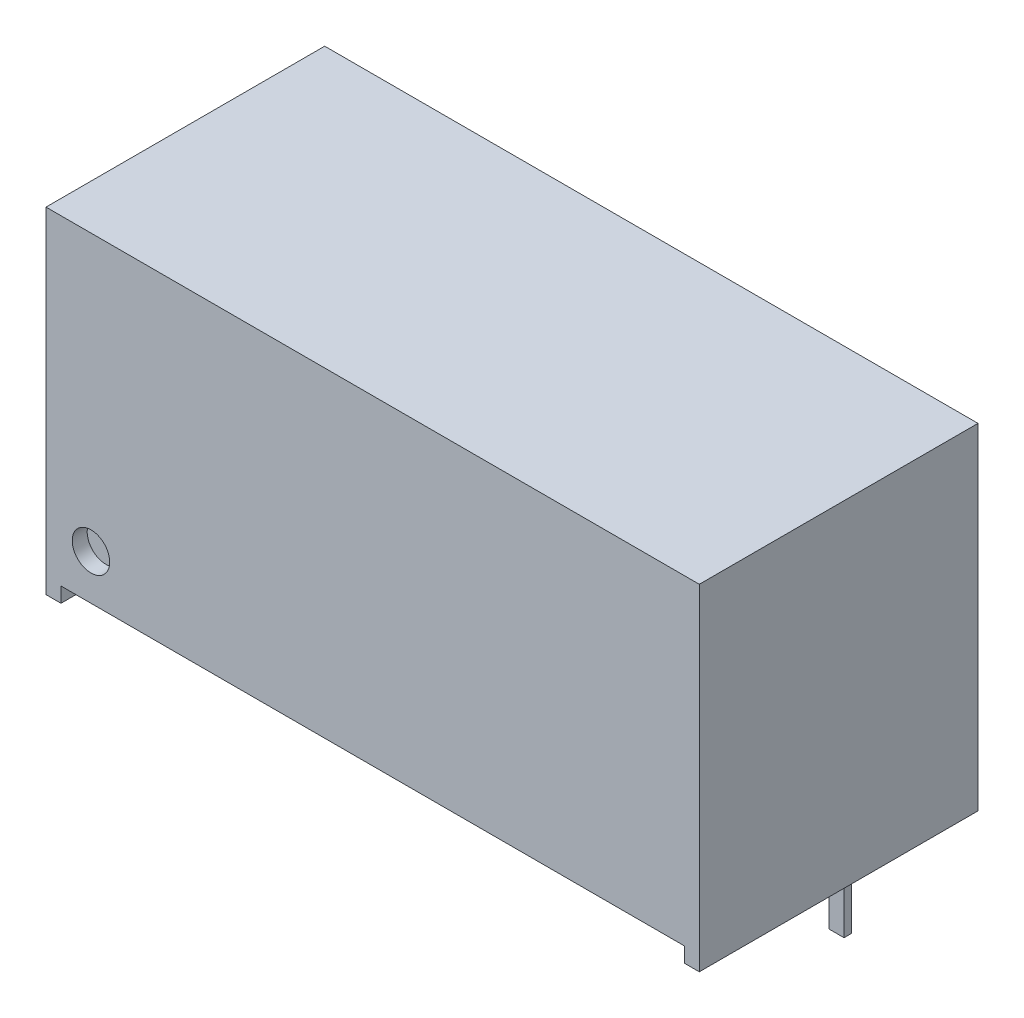
SolidWorks part; units mm, degrees
ref_plane "Front Plane" through (0, 0, 0) normal (0, 0, 1) x (1, 0, 0)
ref_plane "Top Plane" through (0, 0, 0) normal (0, 1, 0) x (1, 0, 0)
ref_plane "Right Plane" through (0, 0, 0) normal (1, 0, 0) x (0, 0, -1)
sketch "Sketch2" plane through (0, 0, 0) normal (0, 0, 1) x (1, 0, 0)
  line L0 (0, 0) -> (0, 11.2)
  line L1 (0, 11.2) -> (21.8, 11.2)
  line L2 (21.8, 11.2) -> (21.8, 0)
  line L3 (21.8, 0) -> (21.3, 0)
  line L4 (21.3, 0) -> (21.3, 0.5)
  line L5 (21.3, 0.5) -> (0.5, 0.5)
  line L6 (0.5, 0.5) -> (0.5, 0)
  line L7 (0.5, 0) -> (0, 0)
  dimension "D1" = 11.2
  dimension "D2" = 21.8
  dimension "D3" = 0.5
  dimension "D4" = 0.5
  dimension "D5" = 0.5
extrude "Boss-Extrude1" add sketch "Sketch2" along normal blind 9.3
sketch "Sketch3" plane through (0, 0.5, 0) normal (0, -1, 0) x (1, 0, 0)
  line L0 (0, 9.3) -> (0, 0) construction
  line L1 (1.75, 2.7) -> (2.25, 2.7)
  line L2 (1.75, 2.7) -> (1.75, 2.45)
  line L3 (1.75, 2.45) -> (2.25, 2.45)
  line L4 (2.25, 2.7) -> (2.25, 2.45)
  line L5 (4.29, 2.7) -> (4.79, 2.7)
  line L6 (4.29, 2.7) -> (4.29, 2.45)
  line L7 (4.29, 2.45) -> (4.79, 2.45)
  line L8 (4.79, 2.7) -> (4.79, 2.45)
  line L9 (6.83, 2.7) -> (7.33, 2.7)
  line L10 (6.83, 2.7) -> (6.83, 2.45)
  line L11 (6.83, 2.45) -> (7.33, 2.45)
  line L12 (7.33, 2.7) -> (7.33, 2.45)
  line L13 (11.91, 2.7) -> (12.41, 2.7)
  line L14 (11.91, 2.7) -> (11.91, 2.45)
  line L15 (11.91, 2.45) -> (12.41, 2.45)
  line L16 (12.41, 2.7) -> (12.41, 2.45)
  line L17 (14.45, 2.7) -> (14.95, 2.7)
  line L18 (14.45, 2.7) -> (14.45, 2.45)
  line L19 (14.45, 2.45) -> (14.95, 2.45)
  line L20 (14.95, 2.7) -> (14.95, 2.45)
  line L21 (16.99, 2.7) -> (17.49, 2.7)
  line L22 (16.99, 2.7) -> (16.99, 2.45)
  line L23 (16.99, 2.45) -> (17.49, 2.45)
  line L24 (17.49, 2.7) -> (17.49, 2.45)
  line L25 (19.53, 2.7) -> (20.03, 2.7)
  line L26 (19.53, 2.7) -> (19.53, 2.45)
  line L27 (19.53, 2.45) -> (20.03, 2.45)
  line L28 (20.03, 2.7) -> (20.03, 2.45)
  line L29 (0.5, 0) -> (21.3, 0) construction
  point P28 (2.25, 2.575)
  point P29 (4.79, 2.575)
  point P30 (7.33, 2.575)
  point P31 (12.41, 2.575)
  point P32 (14.95, 2.575)
  point P33 (17.49, 2.575)
  point P34 (20.03, 2.575)
  point P37 (2, 2.45)
  point P38 (4.54, 2.45)
  point P39 (7.08, 2.45)
  point P40 (4.3782, 3.0313)
  point P41 (12.16, 2.45)
  point P42 (14.7, 2.45)
  point P43 (17.24, 2.45)
  point P44 (19.78, 2.45)
  point P45 (2, 2.7)
  dimension "D1" = 0.5
  dimension "D2" = 0.25
  dimension "D3" = 2
  dimension "D4" = 2.54
  dimension "D5" = 2.54
  dimension "D6" = 5.08
  dimension "D7" = 2.54
  dimension "D8" = 2.54
  dimension "D9" = 2.54
  dimension "D10" = 2.7
extrude "Boss-Extrude2" add sketch "Sketch3" along normal blind 3.7
sketch "Sketch4" plane through (0, 0, 9.3) normal (0, 0, 1) x (1, 0, 0)
  line L0 (0.5, 0.5) -> (21.3, 0.5) construction
  line L2 (0, 11.2) -> (0, 0) construction
  circle A0 centre (1.5, 2) radius 0.625
  point P4 (0, 0)
  point P6 (0, 2.4865)
  dimension "D1" = 1.25
  dimension "D2" = 1.5
  dimension "D3" = 1.5
extrude "Cut-Extrude1" cut sketch "Sketch4" against normal blind 0.5
